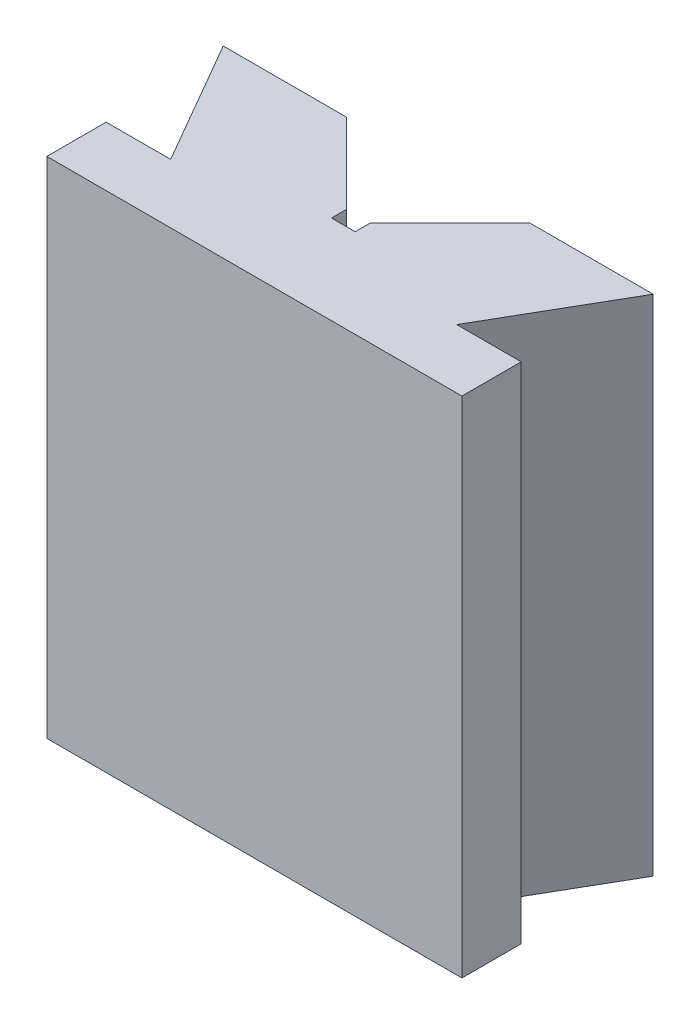
SolidWorks part; units mm, degrees
ref_plane "Přední rovina" through (0, 0, 0) normal (0, 0, 1) x (1, 0, 0)
ref_plane "Vrchní rovina" through (0, 0, 0) normal (0, 1, 0) x (1, 0, 0)
ref_plane "Pravá rovina" through (0, 0, 0) normal (1, 0, 0) x (0, 0, -1)
sketch "Skica1" plane through (0, 0, 0) normal (0, 1, 0) x (1, 0, 0)
  line L8 (0, 0) -> (0, 20)
  line L9 (0, 20) -> (21.7487, 20)
  line L10 (0, 0) -> (140, 0)
  line L11 (21.7487, 20) -> (-2.5, 62)
  line L12 (-2.5, 62) -> (39, 62)
  line L14 (66, 30) -> (74, 30)
  line L15 (70, 30) -> (70, 0) construction
  line L16 (39, 62) -> (66, 35)
  line L17 (66, 35) -> (66, 30)
  line L18 (74, 35) -> (74, 30)
  line L19 (101, 62) -> (74, 35)
  line L20 (142.5, 62) -> (101, 62)
  line L21 (118.2513, 20) -> (142.5, 62)
  line L22 (140, 20) -> (118.2513, 20)
  line L23 (140, 0) -> (140, 20)
  point P2 (0, 0)
  dimension "D1" = 30
  dimension "D2" = 20
  dimension "D3" = 62
  dimension "D4" = 60
  dimension "D5" = 70
  dimension "D6" = 145
  dimension "D7" = 45
  dimension "D8" = 5
  dimension "D9" = 4
extrude "Přidat vysunutím1" add sketch "Skica1" along normal blind 170 contours L16 L17 L14 L18 L19 L20 L21 L22 L23 L10 L8 L9 L11 L12
